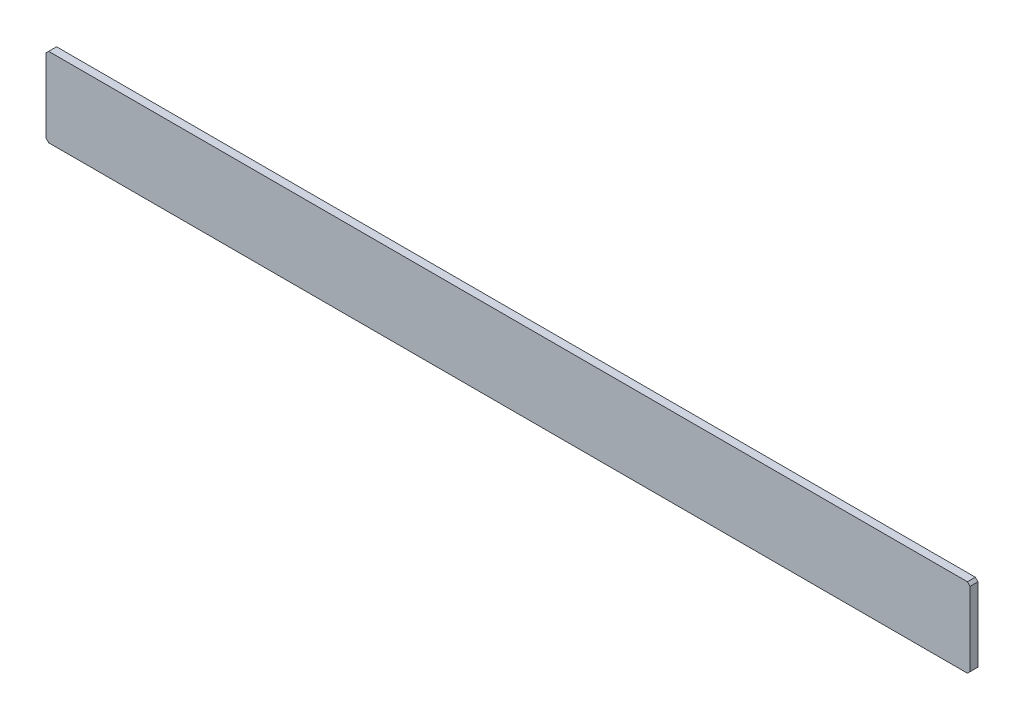
SolidWorks part; units mm, degrees
ref_plane "前视基准面" through (0, 0, 0) normal (0, 0, 1) x (1, 0, 0)
ref_plane "上视基准面" through (0, 0, 0) normal (0, 1, 0) x (1, 0, 0)
ref_plane "右视基准面" through (0, 0, 0) normal (1, 0, 0) x (0, 0, -1)
sketch "草图1" plane through (0, 0, 0) normal (0, 0, 1) x (1, 0, 0)
  line L1 (350, -30) -> (-350, -30)
  line L2 (350, -30) -> (350, 30)
  line L3 (350, 30) -> (-350, 30)
  line L4 (-350, -30) -> (-350, 30)
  line L5 (350, -30) -> (-350, 30) construction
  line L6 (350, 30) -> (-350, -30) construction
  point P0 (0, 0)
  dimension "D1" = 700
  dimension "D2" = 60
extrude "凸台-拉伸1" add sketch "草图1" along normal mid plane 6
chamfer "倒角1" distance 2 angle 45 4 edges at (350, -30, 0) (350, 30, 0) (-350, -30, 0) (-350, 30, 0)
